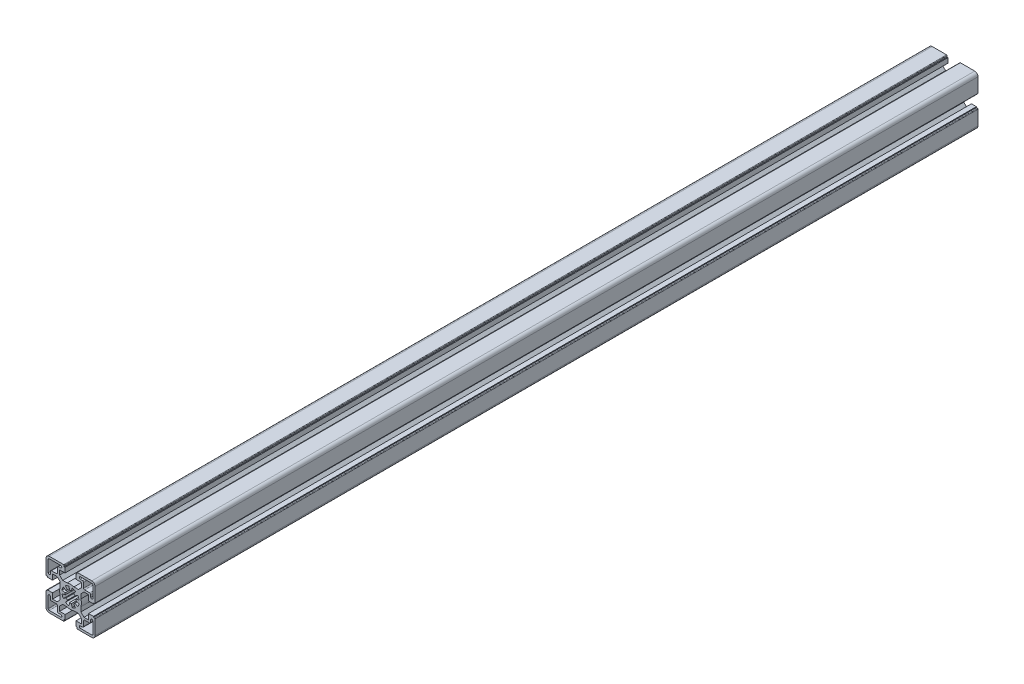
SolidWorks part; units mm, degrees
material "7079 Alloy"
ref_plane "Front Plane" through (0, 0, 0) normal (0, 0, 1) x (1, 0, 0)
ref_plane "Top Plane" through (0, 0, 0) normal (0, 1, 0) x (1, 0, 0)
ref_plane "Right Plane" through (0, 0, 0) normal (1, 0, 0) x (0, 0, -1)
sketch "Sketch1" plane through (0, 0, 0) normal (0, 0, 1) x (1, 0, 0)
  line L0 (0, 34.901) -> (0, -38.8683) construction
  line L1 (-27.7848, 0) -> (42.6814, 0) construction
  line L88 (0.8682, 4.924) -> (1.3892, 7.8784)
  line L89 (-0.8682, 4.924) -> (-1.3892, 7.8785)
  line L90 (-4.5886, 6.5532) -> (-2.8679, 4.0957)
  line L91 (-4.0957, 2.8679) -> (-6.5532, 4.5886)
  line L92 (-7.8784, 1.3892) -> (-4.924, 0.8682)
  line L93 (-7.8785, -1.3892) -> (-4.924, -0.8682)
  line L94 (-6.5532, -4.5886) -> (-4.0957, -2.8679)
  line L95 (-4.5886, -6.5532) -> (-2.8679, -4.0957)
  line L96 (-1.3892, -7.8784) -> (-0.8682, -4.924)
  line L97 (0.8682, -4.924) -> (1.3892, -7.8784)
  line L98 (4.5886, -6.5532) -> (2.8679, -4.0957)
  line L99 (4.0957, -2.8679) -> (6.5532, -4.5886)
  line L100 (7.8784, -1.3892) -> (4.924, -0.8682)
  line L101 (4.924, 0.8682) -> (7.8784, 1.3892)
  line L102 (4.0957, 2.8679) -> (6.5532, 4.5886)
  line L103 (2.8679, 4.0957) -> (4.5886, 6.5532)
  line L104 (-5, -16.4999) -> (-5, -20.9999)
  line L105 (-5, -20.9999) -> (-5.8, -20.9999)
  line L106 (-5.8, -20.9999) -> (-5.8, -22)
  line L107 (-6.3, -22.5) -> (-19.5, -22.5)
  line L108 (-22.5, -19.5) -> (-22.5, -6.2999)
  line L109 (-22, -5.7999) -> (-21, -5.7999)
  line L110 (-21, -5.7999) -> (-21, -4.9999)
  line L111 (-21, -4.9999) -> (-16.5, -4.9999)
  line L112 (-16.5, -4.9999) -> (-16.5, -10.0499)
  line L113 (-16.5, -10.0499) -> (-12.3429, -10.0499)
  line L114 (-12.3429, -10.0499) -> (-9.5, -7.207)
  line L115 (-9.5, -7.207) -> (-9.5, -3.1226)
  line L116 (-9.5, 3.1227) -> (-9.5, 7.207)
  line L117 (-9.5, 7.207) -> (-12.3429, 10.0499)
  line L118 (-12.3429, 10.0499) -> (-16.5, 10.0499)
  line L119 (-16.5, 10.0499) -> (-16.5, 4.9999)
  line L120 (-16.5, 4.9999) -> (-21, 4.9999)
  line L121 (-21, 4.9999) -> (-21, 5.7999)
  line L122 (-21, 5.7999) -> (-22, 5.7999)
  line L123 (-22.5, 6.2999) -> (-22.5, 19.5)
  line L124 (-19.5, 22.5) -> (-6.3, 22.5)
  line L125 (-5.7999, 21.9999) -> (-5.7999, 20.9999)
  line L126 (-5.7999, 20.9999) -> (-5, 20.9999)
  line L127 (-5, 20.9999) -> (-5, 16.5)
  line L128 (-5, 16.5) -> (-10.0501, 16.5)
  line L129 (-10.0501, 16.5) -> (-10.0501, 12.3428)
  line L130 (-10.0501, 12.3428) -> (-7.2072, 9.4999)
  line L131 (-7.2072, 9.4999) -> (-3.1228, 9.4999)
  line L132 (3.1226, 9.4999) -> (7.207, 9.4999)
  line L133 (7.207, 9.4999) -> (10.0499, 12.3428)
  line L134 (10.0499, 12.3428) -> (10.0499, 16.5)
  line L135 (10.0499, 16.5) -> (5, 16.5)
  line L136 (5, 16.5) -> (5, 21)
  line L137 (5, 21) -> (5.7999, 21)
  line L138 (5.7999, 21) -> (5.7999, 21.9999)
  line L139 (6.3, 22.5) -> (19.5001, 22.5)
  line L140 (22.5001, 6.2999) -> (22.5001, 19.5)
  line L141 (22.0001, 5.7999) -> (21, 5.7999)
  line L142 (21, 5.7999) -> (21, 4.9999)
  line L143 (21, 4.9999) -> (16.5, 4.9999)
  line L144 (16.5, 4.9999) -> (16.5, 10.0499)
  line L145 (16.5, 10.0499) -> (12.3429, 10.0499)
  line L146 (12.3429, 10.0499) -> (9.4999, 7.207)
  line L147 (9.4999, 7.207) -> (9.4999, 3.1227)
  line L148 (9.4999, -3.1226) -> (9.4999, -7.207)
  line L149 (9.4999, -7.207) -> (12.3429, -10.0499)
  line L150 (12.3429, -10.0499) -> (16.5, -10.0499)
  line L151 (16.5, -10.0499) -> (16.5, -4.9999)
  line L152 (16.5, -4.9999) -> (21, -4.9999)
  line L153 (21, -4.9999) -> (21, -5.7999)
  line L154 (21, -5.7999) -> (22.0001, -5.7999)
  line L155 (22.5001, -6.2999) -> (22.5001, -19.5)
  line L156 (6.3, -22.5) -> (19.5001, -22.5)
  line L157 (5.8, -22) -> (5.8, -20.9999)
  line L158 (5.8, -20.9999) -> (5, -20.9999)
  line L159 (5, -20.9999) -> (5, -16.4999)
  line L160 (5, -16.4999) -> (10.0499, -16.4999)
  line L161 (10.0499, -16.4999) -> (10.0499, -12.3428)
  line L162 (10.0499, -12.3428) -> (7.2069, -9.4998)
  line L163 (7.2069, -9.4998) -> (3.1226, -9.4998)
  line L164 (-3.1228, -9.4998) -> (-7.2071, -9.4998)
  line L165 (-7.2071, -9.4998) -> (-10.0501, -12.3428)
  line L166 (-10.0501, -12.3428) -> (-10.0501, -16.4999)
  line L167 (-10.0501, -16.4999) -> (-5, -16.4999)
  line L168 (-17.5001, -12) -> (-13.0001, -12)
  line L169 (-12.0001, -17.4999) -> (-12.0001, -13)
  line L170 (-11.0001, -18.4999) -> (-9.0001, -18.4999)
  line L171 (-19.5001, -20.5) -> (-9.0001, -20.5)
  line L172 (-20.5001, -19.5) -> (-20.5001, -8.9999)
  line L173 (-18.5001, -11) -> (-18.5001, -8.9999)
  line L174 (13, -12) -> (17.5, -12)
  line L175 (12, -17.4999) -> (12, -13)
  line L176 (9, -18.4999) -> (11, -18.4999)
  line L177 (9, -20.5) -> (19.5, -20.5)
  line L178 (20.5, -19.5) -> (20.5, -9.0001)
  line L179 (18.5, -11) -> (18.5, -9.0001)
  line L180 (-17.5001, 12) -> (-13.0001, 12)
  line L181 (-12.0001, 13) -> (-12.0001, 17.4999)
  line L182 (-11.0001, 18.4999) -> (-9.0001, 18.4999)
  line L183 (-19.5001, 20.5) -> (-9.0001, 20.5)
  line L184 (-20.5001, 8.9999) -> (-20.5001, 19.5)
  line L185 (-18.5001, 8.9999) -> (-18.5001, 11)
  line L186 (13, 12) -> (17.5, 12)
  line L187 (12, 13) -> (12, 17.4999)
  line L188 (9, 18.4999) -> (11, 18.4999)
  line L189 (9, 20.5) -> (19.5, 20.5)
  line L190 (20.5, 9.0001) -> (20.5, 19.5)
  line L191 (18.5, 9.0001) -> (18.5, 11)
  arc A56 (0.8682, 4.924) -> (-0.8682, 4.924) centre (0, 0) ccw
  arc A57 (-1.3892, 7.8785) -> (-4.5886, 6.5532) centre (0, 0) ccw
  arc A58 (-2.8679, 4.0957) -> (-4.0957, 2.8679) centre (0, 0) ccw
  arc A59 (-6.5532, 4.5886) -> (-7.8784, 1.3892) centre (0, 0) ccw
  arc A60 (-4.924, 0.8682) -> (-4.924, -0.8682) centre (0, 0) ccw
  arc A61 (-7.8785, -1.3892) -> (-6.5532, -4.5886) centre (0, 0) ccw
  arc A62 (-4.0957, -2.8679) -> (-2.8679, -4.0957) centre (0, 0) ccw
  arc A63 (-4.5886, -6.5532) -> (-1.3892, -7.8784) centre (0, 0) ccw
  arc A64 (-0.8682, -4.924) -> (0.8682, -4.924) centre (0, 0) ccw
  arc A65 (1.3892, -7.8784) -> (4.5886, -6.5532) centre (0, 0) ccw
  arc A66 (2.8679, -4.0957) -> (4.0957, -2.8679) centre (0, 0) ccw
  arc A67 (6.5532, -4.5886) -> (7.8784, -1.3892) centre (0, 0) ccw
  arc A68 (4.924, -0.8682) -> (4.924, 0.8682) centre (0, 0) ccw
  arc A69 (7.8784, 1.3892) -> (6.5532, 4.5886) centre (0, 0) ccw
  arc A70 (4.0957, 2.8679) -> (2.8679, 4.0957) centre (0, 0) ccw
  arc A71 (4.5886, 6.5532) -> (1.3892, 7.8784) centre (0, 0) ccw
  arc A72 (-6.3, -22.5) -> (-5.8, -22) centre (-6.3, -22) ccw
  arc A73 (-22.5, -19.5) -> (-19.5, -22.5) centre (-19.5, -19.5) ccw
  arc A74 (-22, -5.7999) -> (-22.5, -6.2999) centre (-22, -6.2999) ccw
  arc A75 (-9.5, 3.1227) -> (-9.5, -3.1226) centre (0, 0.0001) ccw
  arc A76 (-22.5, 6.2999) -> (-22, 5.7999) centre (-22, 6.2999) ccw
  arc A77 (-19.5, 22.5) -> (-22.5, 19.5) centre (-19.5, 19.5) ccw
  arc A78 (-5.7999, 21.9999) -> (-6.3, 22.5) centre (-6.3, 21.9999) ccw
  arc A79 (3.1226, 9.4999) -> (-3.1228, 9.4999) centre (-0.0001, -0.0001) ccw
  arc A80 (6.3, 22.5) -> (5.7999, 21.9999) centre (6.3, 21.9999) ccw
  arc A81 (22.5001, 19.5) -> (19.5001, 22.5) centre (19.5001, 19.5) ccw
  arc A82 (22.0001, 5.7999) -> (22.5001, 6.2999) centre (22.0001, 6.2999) ccw
  arc A83 (9.4999, -3.1226) -> (9.4999, 3.1227) centre (0, 0.0001) ccw
  arc A84 (22.5001, -6.2999) -> (22.0001, -5.7999) centre (22.0001, -6.2999) ccw
  arc A85 (19.5001, -22.5) -> (22.5001, -19.5) centre (19.5001, -19.5) ccw
  arc A86 (5.8, -22) -> (6.3, -22.5) centre (6.3, -22) ccw
  arc A87 (-3.1228, -9.4998) -> (3.1226, -9.4998) centre (-0.0001, 0.0001) ccw
  arc A88 (-18.5001, -11) -> (-17.5001, -12) centre (-17.5001, -11) ccw
  arc A89 (-12.0001, -13) -> (-13.0001, -12) centre (-13.0001, -13) ccw
  arc A90 (-12.0001, -17.4999) -> (-11.0001, -18.4999) centre (-11.0001, -17.4999) ccw
  arc A91 (-9.0001, -20.5) -> (-9.0001, -18.4999) centre (-9.0001, -19.5) ccw
  arc A92 (-20.5001, -19.5) -> (-19.5001, -20.5) centre (-19.5001, -19.5) ccw
  arc A93 (-18.5001, -8.9999) -> (-20.5001, -8.9999) centre (-19.5001, -8.9999) ccw
  arc A94 (17.5, -12) -> (18.5, -11) centre (17.5, -11) ccw
  arc A95 (13, -12) -> (12, -13) centre (13, -13) ccw
  arc A96 (11, -18.4999) -> (12, -17.4999) centre (11, -17.4999) ccw
  arc A97 (9, -18.4999) -> (9, -20.5) centre (9, -19.5) ccw
  arc A98 (19.5, -20.5) -> (20.5, -19.5) centre (19.5, -19.5) ccw
  arc A99 (20.5, -9.0001) -> (18.5, -9.0001) centre (19.5, -9.0001) ccw
  arc A100 (-17.5001, 12) -> (-18.5001, 11) centre (-17.5001, 11) ccw
  arc A101 (-13.0001, 12) -> (-12.0001, 13) centre (-13.0001, 13) ccw
  arc A102 (-11.0001, 18.4999) -> (-12.0001, 17.4999) centre (-11.0001, 17.4999) ccw
  arc A103 (-9.0001, 18.4999) -> (-9.0001, 20.5) centre (-9.0001, 19.5) ccw
  arc A104 (-19.5001, 20.5) -> (-20.5001, 19.5) centre (-19.5001, 19.5) ccw
  arc A105 (-20.5001, 8.9999) -> (-18.5001, 8.9999) centre (-19.5001, 8.9999) ccw
  arc A106 (18.5, 11) -> (17.5, 12) centre (17.5, 11) ccw
  arc A107 (12, 13) -> (13, 12) centre (13, 13) ccw
  arc A108 (12, 17.4999) -> (11, 18.4999) centre (11, 17.4999) ccw
  arc A109 (9, 20.5) -> (9, 18.4999) centre (9, 19.5) ccw
  arc A110 (20.5, 19.5) -> (19.5, 20.5) centre (19.5, 19.5) ccw
  arc A111 (18.5, 9.0001) -> (20.5, 9.0001) centre (19.5, 9.0001) ccw
  dimension "D5" = 10
  dimension "D1" = 45.0001
  dimension "D2" = 44.9999
  dimension "D3" = 12.5001
  dimension "D4" = 10
  dimension "D6" = 22.5001
extrude "Base-Extrude" add sketch "Sketch1" along normal blind 810
